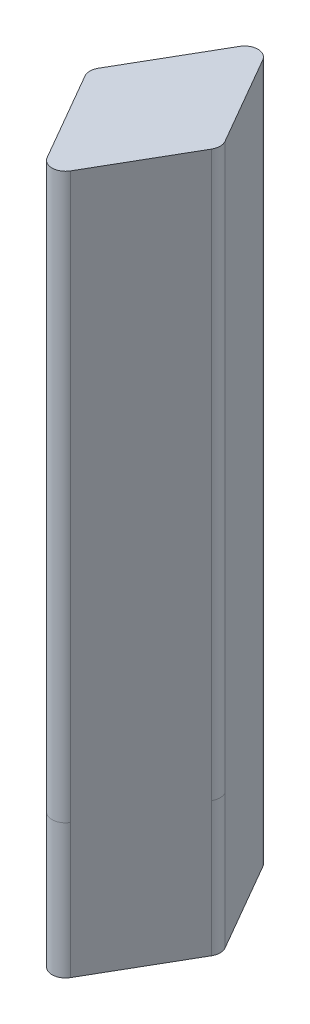
SolidWorks part; units mm, degrees
material "ABS"
ref_plane "Front Plane" through (0, 0, 0) normal (0, 0, 1) x (1, 0, 0)
ref_plane "Top Plane" through (0, 0, 0) normal (0, 1, 0) x (1, 0, 0)
ref_plane "Right Plane" through (0, 0, 0) normal (1, 0, 0) x (0, 0, -1)
sketch "Sketch1" plane through (0, 0, 0) normal (0, 1, 0) x (1, 0, 0)
  line L0 (-5, 0) -> (0, 8.6603)
  line L1 (0, 8.6603) -> (5, 0)
  line L2 (5, 0) -> (0, -8.6603)
  line L3 (0, -8.6603) -> (-5, 0)
  line L4 (-5, 0) -> (5, 0) construction
  line L5 (0, 8.6603) -> (0, -8.6603) construction
  line L6 (-22, 0) -> (22, 0) construction
  point P2 (0, 0)
  dimension "D1" = 60
  dimension "D2" = 60
  dimension "D3" = 120
  dimension "D4" = 10
extrude "Boss-Extrude1" add sketch "Sketch1" against normal blind 52
sketch "Sketch2" plane through (0, 0, 0) normal (0, 1, 0) x (1, 0, 0)
  line L0 (0, 6.6603) -> (-3.8453, 0)
  line L1 (-3.8453, 0) -> (0, -6.6603)
  line L2 (0, -6.6603) -> (3.8453, 0)
  line L3 (3.8453, 0) -> (0, 6.6603)
  line L4 (0, 8.6603) -> (-5, 0) construction
  line L5 (-5, 0) -> (0, -8.6603) construction
  line L6 (0, -8.6603) -> (5, 0) construction
  line L7 (5, 0) -> (0, 8.6603) construction
  dimension "D1" = 1
  dimension "D2" = 1
  dimension "D3" = 1
  dimension "D4" = 1
extrude "Cut-Extrude1" cut sketch "Sketch2" against normal blind 45
sketch "Sketch3" plane through (0, -45, 0) normal (0, 1, 0) x (1, 0, 0)
  circle A0 centre (0, 0) radius 1.5
  dimension "D1" = 3
extrude "Cut-Extrude2" cut sketch "Sketch3" against normal through all
sketch "Sketch4" plane through (0, 0, 0) normal (0, 0, 1) x (1, 0, 0)
  line L0 (0, -45) -> (0, -55)
  dimension "D1" = 10
sketch "Sketch5" plane through (0, 0, 0) normal (0, 1, 0) x (1, 0, 0)
  line L0 (-3.8453, 0) -> (0, 6.6603)
  line L1 (0, 6.6603) -> (3.8453, 0)
  line L2 (3.8453, 0) -> (0, -6.6603)
  line L3 (0, -6.6603) -> (-3.8453, 0)
extrude "Boss-Extrude2" add sketch "Sketch5" against normal blind 1
sketch "Sketch7" plane through (0, 0, 0) normal (0, 0, 1) x (1, 0, 0)
  line L0 (0, -55) -> (11.9917, -55)
sketch "Sketch8" plane through (0, -52, 0) normal (0, -1, 0) x (1, 0, 0)
  line L0 (0, 8.6603) -> (-5, 0)
  line L1 (-5, 0) -> (0, -8.6603)
  line L2 (0, -8.6603) -> (5, 0)
  line L3 (5, 0) -> (0, 8.6603)
sketch "Sketch11" plane through (0, -45, 0) normal (0, 1, 0) x (1, 0, 0)
  circle A0 centre (0, 0) radius 3.25
  circle A1 centre (0, 0) radius 2
  dimension "D1" = 6.5
  dimension "D2" = 4
extrude "Cut-Extrude3" [suppressed] cut sketch "Sketch11" against normal blind 8
sketch "Sketch12" plane through (0, -52, 0) normal (0, -1, 0) x (1, 0, 0)
  line L0 (-5, 0) -> (5, 0) construction
  line L1 (0, 8.6603) -> (0, 7.6603) construction
  line L6 (0, -7.6603) -> (0, -8.6603) construction
  line L7 (-0.866, 7.1603) -> (0, 8.6603)
  line L8 (0, 8.6603) -> (0.866, 7.1603)
  line L9 (-4.7113, 0.5) -> (-5, 0)
  line L10 (-5, 0) -> (-4.7113, -0.5)
  line L11 (-0.866, -7.1603) -> (0, -8.6603)
  line L12 (0, -8.6603) -> (0.866, -7.1603)
  line L13 (4.7113, 0.5) -> (5, 0)
  line L14 (5, 0) -> (4.7113, -0.5)
  arc A0 (4.7113, 0.5) -> (4.7113, -0.5) centre (3.8453, 0) cw
  arc A1 (0.866, -7.1603) -> (-0.866, -7.1603) centre (0, -6.6603) cw
  arc A2 (-4.7113, -0.5) -> (-4.7113, 0.5) centre (-3.8453, 0) cw
  arc A3 (-0.866, 7.1603) -> (0.866, 7.1603) centre (0, 6.6603) cw
  dimension "D1" = 1
extrude "Cut-Extrude5" cut sketch "Sketch12" against normal blind 10
fillet "Fillet1" radius 1 4 edges at (-5, -21, 0) (0, -21, 8.6603) (5, -21, 0) (0, -21, -8.6603)
